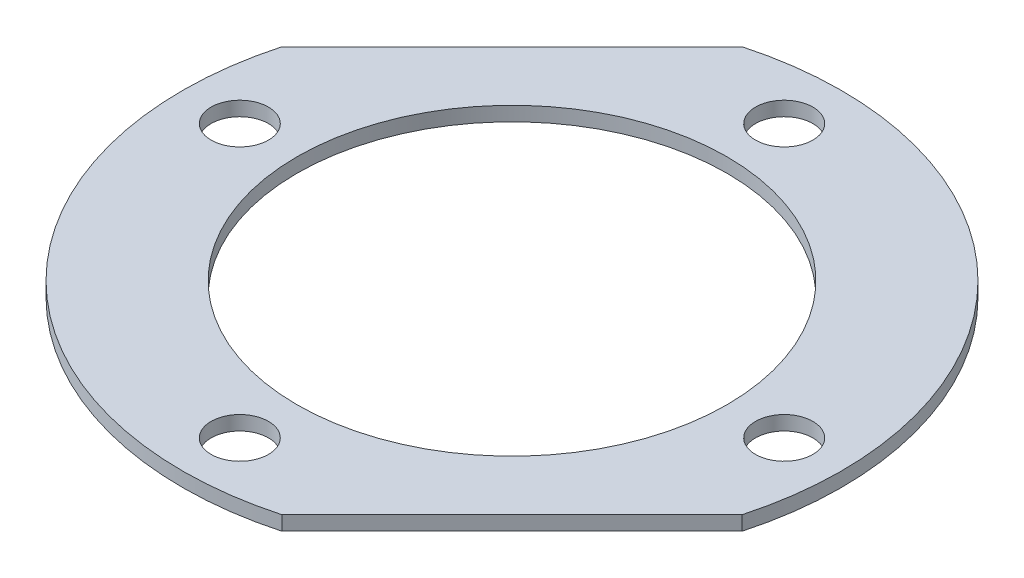
SolidWorks part; units mm, degrees
material "PTFE (general)"
ref_plane "Front Plane" through (0, 0, 0) normal (0, 0, 1) x (1, 0, 0)
ref_plane "Top Plane" through (0, 0, 0) normal (0, 1, 0) x (1, 0, 0)
ref_plane "Right Plane" through (0, 0, 0) normal (1, 0, 0) x (0, 0, -1)
sketch "Sketch2" plane through (0, 0, 0) normal (0, 1, 0) x (1, 0, 0)
  line L0 (0, 0) -> (16.2635, 16.2635)
  line L1 (16.2635, 16.2635) -> (30.4056, 2.1213)
  line L2 (16.2635, 16.2635) -> (2.1213, 30.4056)
  line L3 (0, 0) -> (-16.2635, -16.2635)
  line L4 (-16.2635, -16.2635) -> (-2.1213, -30.4056)
  line L5 (-16.2635, -16.2635) -> (-30.4056, -2.1213)
  line L6 (-2.1213, -30.4056) -> (30.4056, 2.1213)
  line L7 (2.1213, 30.4056) -> (-30.4056, -2.1213)
  line L8 (0, 0) -> (19, 0)
  line L9 (0, 0) -> (-19, 0)
  line L10 (0, 0) -> (0, 19)
  line L11 (0, 0) -> (0, -19)
  circle A0 centre (0, 0) radius 23
  circle A1 centre (19, 0) radius 2
  circle A2 centre (-19, 0) radius 2
  circle A3 centre (0, 19) radius 2
  circle A4 centre (0, -19) radius 2
  circle A5 centre (0, 0) radius 15
  dimension "D1" = 46
  dimension "D9" = 19
  dimension "D12" = 4
  dimension "D13" = 4
  dimension "D14" = 4
  dimension "D15" = 4
  dimension "D2" = 20
  dimension "D3" = 20
  dimension "D4" = 20
  dimension "D5" = 20
  dimension "D6" = 46
  dimension "D7" = 46
  dimension "D8" = 19
  dimension "D10" = 19
  dimension "D11" = 19
extrude "Boss-Extrude1" add sketch "Sketch2" along normal blind 1
